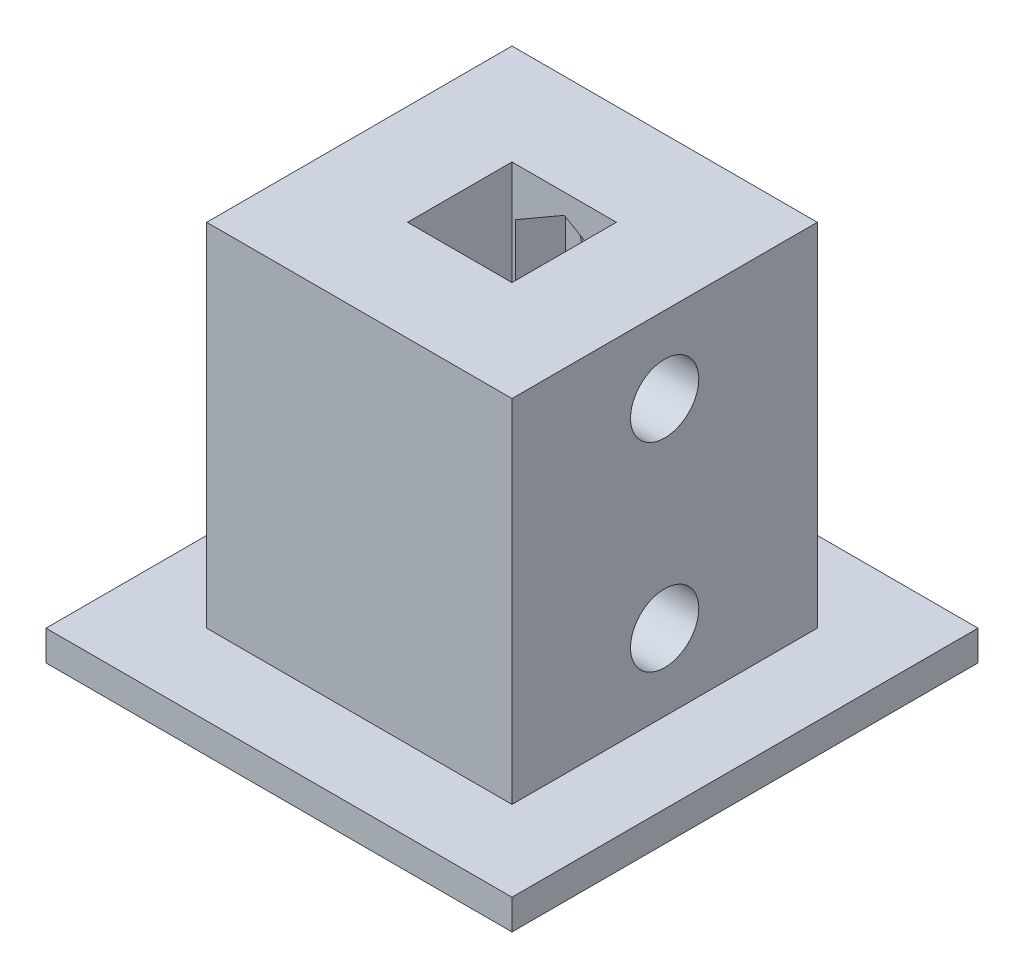
SolidWorks part; units mm, degrees
ref_plane "Front Plane" through (0, 0, 0) normal (0, 0, 1) x (1, 0, 0)
ref_plane "Top Plane" through (0, 0, 0) normal (0, 1, 0) x (1, 0, 0)
ref_plane "Right Plane" through (0, 0, 0) normal (1, 0, 0) x (0, 0, -1)
sketch "Sketch1" plane through (0, 0, 0) normal (0, 1, 0) x (1, 0, 0)
  line L0 (10.4, 0) -> (20.4, 0) construction
  line L1 (0, 0) -> (10.4, 0)
  line L2 (0, 0) -> (0, 10.4)
  line L3 (0, 10.4) -> (10.4, 10.4)
  line L4 (10.4, 0) -> (10.4, 10.4)
  line L5 (-10, -10) -> (20.4, -10)
  line L6 (-10, -10) -> (-10, 20.4)
  line L7 (-10, 20.4) -> (20.4, 20.4)
  line L8 (20.4, -10) -> (20.4, 20.4)
  line L9 (10.4, 10.4) -> (10.4, 20.4) construction
  line L10 (0, 0) -> (0, -10) construction
  line L11 (0, 10.4) -> (-10, 10.4) construction
  dimension "D1" = 10
  dimension "D2" = 10.4
  dimension "D3" = 10.4
extrude "Boss-Extrude1" add sketch "Sketch1" along normal blind 35
sketch "Sketch2" plane through (10.4, 0, 0) normal (-1, 0, 0) x (0, 0, 1)
  line L0 (-5.2, 35) -> (-5.2, 0) construction
  line L1 (-5.2, 33) -> (-10.0497, 30.2)
  line L2 (-10.0497, 30.2) -> (-10.0497, 24.6)
  line L3 (-10.0497, 24.6) -> (-5.2, 21.8)
  line L4 (-5.2, 21.8) -> (-0.3503, 24.6)
  line L5 (-0.3503, 24.6) -> (-0.3503, 30.2)
  line L6 (-0.3503, 30.2) -> (-5.2, 33)
  line L7 (0, 35) -> (-10.4, 35) construction
  line L8 (0, 0) -> (-10.4, 0) construction
  line L9 (-4.2, 17.5) -> (10, 17.5) construction
  line L11 (-0.3503, 10.4) -> (-0.3503, 4.8)
  line L12 (-5.2, 13.2) -> (-0.3503, 10.4)
  line L13 (-10.0497, 10.4) -> (-5.2, 13.2)
  line L14 (-10.0497, 4.8) -> (-10.0497, 10.4)
  line L15 (-5.2, 2) -> (-10.0497, 4.8)
  line L16 (-0.3503, 4.8) -> (-5.2, 2)
  circle A0 centre (-5.2, 27.4) radius 4.8497 construction
  dimension "D1" = 11.2
  dimension "D2" = 2
extrude "Cut-Extrude1" cut sketch "Sketch2" against normal blind 5
sketch "Sketch3" plane through (15.4, 0, 0) normal (-1, 0, 0) x (0, 0, 1)
  line L0 (-10.0497, 27.4) -> (-0.3503, 27.4) construction
  line L1 (-10.0497, 30.2) -> (-10.0497, 24.6) construction
  line L2 (-0.3503, 24.6) -> (-0.3503, 30.2) construction
  line L3 (-0.3503, 7.6) -> (-10.0497, 7.6) construction
  line L4 (-0.3503, 4.8) -> (-0.3503, 10.4) construction
  line L5 (-10.0497, 10.4) -> (-10.0497, 4.8) construction
  circle A0 centre (-5.2, 27.4) radius 3.4
  circle A1 centre (-5.2, 7.6) radius 3.4
  dimension "D1" = 6.8
extrude "Cut-Extrude2" cut sketch "Sketch3" against normal through all
sketch "Sketch4" plane through (10.4, 0, 0) normal (-1, 0, 0) x (0, 0, 1)
  line L1 (0, 35) -> (0, 0) construction
  line L2 (0, 22.5) -> (0, 12.5)
  line L3 (-1, 22) -> (-1, 13) construction
  line L4 (0, 17.5) -> (-4.4493, 17.5) construction
  line L5 (0, 35) -> (0, 0)
  spline S0 degree 3 poles (0, 22.5) (-2.1122, 21.9525) (-1.8878, 17.5) (-2.1122, 13.0475) (0, 12.5) knots 0 0 0 0 0.5 1 1 1 1
  point P5 (0, 17.5)
  point P7 (-1, 17.5)
  point P20 (0, 17.5)
  dimension "D1" = 2
  dimension "D2" = 10
  dimension "D3" = 9
  dimension "D4" = 1
extrude "Boss-Extrude3" add sketch "Sketch4" along normal up to surface (10.4 mm away) contours L2 S0 up to face at (0, 17.5, -5.2)
sketch "Sketch6" plane through (0, 0, -10.4) normal (0, 0, 1) x (1, 0, 0)
  line L0 (0, 12.5) -> (0, 22.5)
  line L1 (1, 22) -> (1, 13) construction
  line L2 (2, 17.5) -> (0, 17.5) construction
  line L3 (0, 35) -> (0, 0)
  line L5 (0, 35) -> (0, 0) construction
  spline S0 degree 3 poles (0, 12.5) (2.1122, 13.0475) (1.8878, 17.5) (2.1122, 21.9525) (0, 22.5) knots 0 0 0 0 0.5 1 1 1 1
  point P3 (0, 17.5)
  point P10 (1, 17.5)
  point P20 (0, 17.5)
  dimension "D1" = 9
  dimension "D2" = 2
  dimension "D3" = 1
  dimension "D4" = 10
extrude "Boss-Extrude4" add sketch "Sketch6" along normal up to surface (10.4 mm away) contours L0 S0 up to face at (5.2, 28.75, 0)
sketch "Sketch7" plane through (0, 0, -10.4) normal (0, 0, 1) x (1, 0, 0)
  line L0 (5.2, 35) -> (5.2, 0) construction
  line L1 (5.2, 33) -> (0.3503, 30.2)
  line L2 (0.3503, 30.2) -> (0.3503, 24.6)
  line L3 (0.3503, 24.6) -> (5.2, 21.8)
  line L4 (5.2, 21.8) -> (10.0497, 24.6)
  line L5 (10.0497, 24.6) -> (10.0497, 30.2)
  line L6 (10.0497, 30.2) -> (5.2, 33)
  line L7 (6.0321, 17.5) -> (20.2321, 17.5) construction
  line L8 (10.0497, 10.4) -> (10.0497, 4.8)
  line L9 (5.2, 13.2) -> (10.0497, 10.4)
  line L10 (0.3503, 10.4) -> (5.2, 13.2)
  line L11 (0.3503, 4.8) -> (0.3503, 10.4)
  line L12 (5.2, 2) -> (0.3503, 4.8)
  line L13 (10.0497, 4.8) -> (5.2, 2)
  line L14 (10.4, 30.2) -> (10.4, 24.6) construction
  line L15 (10.4, 24.6) -> (10.4, 21.8) construction
  line L16 (10.4, 33) -> (10.4, 30.2) construction
  line L17 (10.4, 30.2) -> (10.4, 24.6)
  line L18 (10.4, 24.6) -> (10.4, 21.8)
  line L19 (10.4, 33) -> (10.4, 30.2)
  line L20 (5.2, 33) -> (10.0497, 33) construction
  line L21 (10.0497, 33) -> (10.0497, 30.2) construction
  line L23 (10.4, 35) -> (0, 35) construction
  line L28 (-10, 0) -> (20.4, 0)
  line L29 (-10, 35) -> (-10, 0)
  line L30 (20.4, 35) -> (-10, 35)
  line L31 (20.4, 0) -> (20.4, 35)
  line L32 (-10, 0) -> (20.4, 0)
  line L33 (-10, 35) -> (-10, 0)
  line L34 (20.4, 35) -> (-10, 35)
  line L35 (20.4, 0) -> (20.4, 35)
  circle A0 centre (5.2, 27.4) radius 4.8497 construction
  point P11 (5.2, 17.5)
  point P36 (-10, 17.5)
  dimension "D1" = 0
extrude "Cut-Extrude3" cut sketch "Sketch7" against normal blind 5 contours L5 L6 L1 L2 L3 L4 | L13 L8 L9 L10 L11 L12
sketch "Sketch8" plane through (0, 0, -15.4) normal (0, 0, 1) x (1, 0, 0)
  line L0 (15.4, 30.8) -> (15.4, 24) construction
  line L1 (15.4, 30.8) -> (15.4, 24)
  line L2 (15.4, 30.8) -> (8.3313, 30.8) construction
  line L3 (15.4, 24) -> (10.7778, 24) construction
  line L4 (5.2, 33) -> (5.2, 21.8) construction
  line L5 (-10, 17.5) -> (20.4, 17.5) construction
  line L9 (-10, 0) -> (20.4, 0)
  line L10 (-10, 35) -> (-10, 0)
  line L11 (20.4, 35) -> (-10, 35)
  line L12 (20.4, 0) -> (20.4, 35)
  line L13 (-10, 0) -> (20.4, 0)
  line L14 (-10, 35) -> (-10, 0)
  line L15 (20.4, 35) -> (-10, 35)
  line L16 (20.4, 0) -> (20.4, 35)
  circle A0 centre (5.2, 27.4) radius 3.4
  circle A1 centre (5.2, 7.6) radius 3.4
  dimension "D1" = 0
extrude "Cut-Extrude4" cut sketch "Sketch8" against normal through all contours A0 | A1
sketch "Sketch9" plane through (0, 0, 0) normal (0, -1, 0) x (1, 0, 0)
  line L0 (5.2, 10) -> (5.2, 18) construction
  line L1 (28.4, 18) -> (-18, 18)
  line L2 (28.4, 18) -> (28.4, -28.4)
  line L3 (28.4, -28.4) -> (-18, -28.4)
  line L4 (-18, 18) -> (-18, -28.4)
  line L5 (-10, 10) -> (20.4, 10) construction
  line L6 (20.4, -5.2) -> (28.4, -5.2) construction
  line L7 (20.4, 10) -> (20.4, -20.4) construction
  line L8 (5.2, -20.4) -> (5.2, -28.4) construction
  line L9 (20.4, -20.4) -> (-10, -20.4) construction
  line L10 (-10, -5.2) -> (-18, -5.2) construction
  line L11 (-10, -20.4) -> (-10, 10) construction
  line L13 (10.4, 0) -> (0, 0)
  line L14 (10.4, 0) -> (10.4, -10.4)
  line L15 (10.4, -10.4) -> (0, -10.4)
  line L16 (0, 0) -> (0, -10.4)
  dimension "D1" = 8
extrude "Boss-Extrude7" add sketch "Sketch9" along normal blind 3
equation "\"8mm hole\" = 8.4mm"
equation "\"22mm hole\"= 23mm"
equation "\"15mm hole\"= 15.8mm"
equation "\"bed height offset\"= 3mm"
equation "\"motor width\"= 42.5mm"
equation "\"D2@Sketch1\"=\"8mm hole\" + 2"
equation "\"D3@Sketch1\"=\"8mm hole\" + 2"
